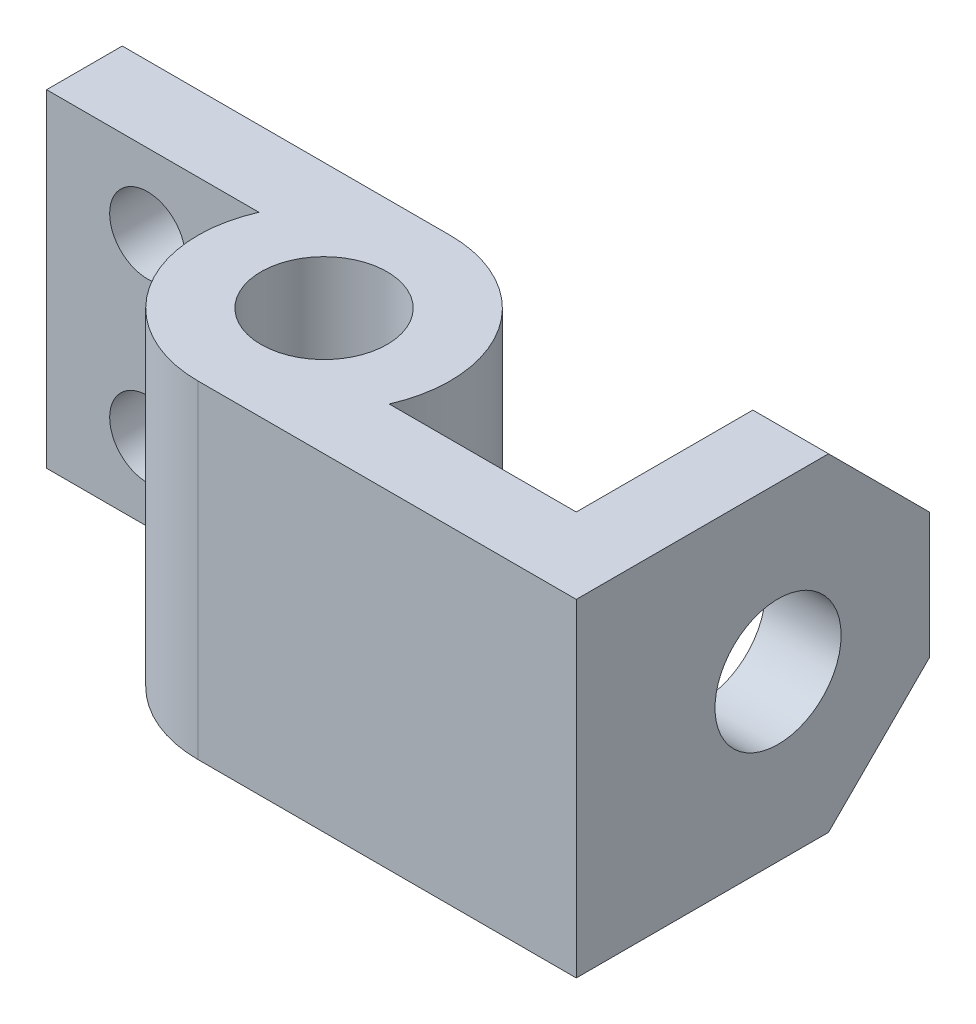
SolidWorks part; units mm, degrees
ref_plane "Front Plane" through (0, 0, 0) normal (0, 0, 1) x (1, 0, 0)
ref_plane "Top Plane" through (0, 0, 0) normal (0, 1, 0) x (1, 0, 0)
ref_plane "Right Plane" through (0, 0, 0) normal (1, 0, 0) x (0, 0, -1)
sketch "Sketch1" plane through (0, 0, 0) normal (0, 1, 0) x (1, 0, 0)
  line L0 (0, 31.75) -> (-82.55, 31.75)
  line L1 (-82.55, 31.75) -> (-82.55, 12.7)
  line L2 (-82.55, 12.7) -> (-29.0994, 12.7)
  line L3 (0, -31.75) -> (95.25, -31.75)
  line L4 (95.25, -31.75) -> (95.25, 57.15)
  line L5 (95.25, 57.15) -> (76.2, 57.15)
  line L6 (76.2, 57.15) -> (76.2, -12.7)
  line L7 (76.2, -12.7) -> (29.0994, -12.7)
  arc A0 (-29.0994, 12.7) -> (0, -31.75) centre (0, 0) ccw
  circle A1 centre (0, 0) radius 15.875
  arc A2 (29.0994, -12.7) -> (0, 31.75) centre (0, 0) ccw
extrude "Boss-Extrude1" add sketch "Sketch1" along normal blind 82.55
sketch "Sketch2" plane through (95.25, 0, 0) normal (1, 0, 0) x (0, 0, -1)
  line L0 (-31.75, 0) -> (19.05, 0) construction
  line L1 (-31.75, 0) -> (57.15, 0) construction
  line L2 (19.05, 0) -> (19.05, 41.402) construction
  circle A0 centre (19.05, 41.402) radius 15.875
extrude "Cut-Extrude1" cut sketch "Sketch2" against normal blind 41.402
sketch "Sketch3" plane through (0, 0, -31.75) normal (0, 0, -1) x (-1, 0, 0)
  line L0 (82.55, 0) -> (57.15, 0) construction
  line L1 (0, 0) -> (82.55, 0) construction
  line L2 (57.15, 0) -> (57.15, 19.05) construction
  line L3 (82.55, 82.55) -> (57.15, 82.55) construction
  line L4 (0, 82.55) -> (82.55, 82.55) construction
  line L5 (57.15, 82.55) -> (57.15, 63.5) construction
  circle A0 centre (57.15, 63.5) radius 9.525
  circle A1 centre (57.15, 19.05) radius 9.525
extrude "Cut-Extrude2" cut sketch "Sketch3" against normal blind 41.402
chamfer "Chamfer1" distance 25.4 angle 45 1 edges at (85.725, 82.55, -57.15)
chamfer "Chamfer2" distance 25.4 angle 45 1 edges at (85.725, 0, -57.15)
